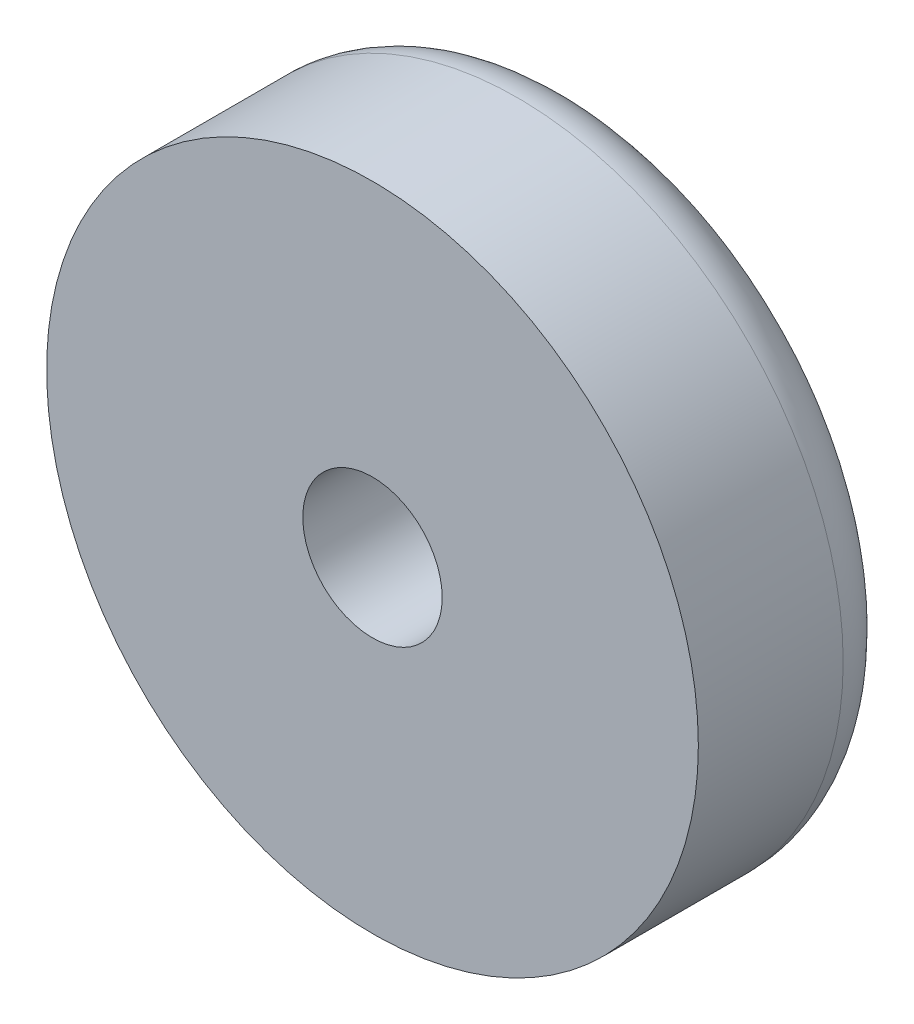
SolidWorks part; units mm, degrees
ref_plane "Front Plane" through (0, 0, 0) normal (0, 0, 1) x (1, 0, 0)
ref_plane "Top Plane" through (0, 0, 0) normal (0, 1, 0) x (1, 0, 0)
ref_plane "Right Plane" through (0, 0, 0) normal (1, 0, 0) x (0, 0, -1)
sketch "Sketch3" plane through (0, 0, 0) normal (0, 1, 0) x (1, 0, 0)
  line L0 (0, 0) -> (0, 3.16) construction
  line L1 (0, 3.16) -> (3.85, 3.16)
  line L2 (3.85, 0) -> (18, 0)
  line L3 (3.85, 3.16) -> (3.85, 0)
  line L4 (0, 3.16) -> (0, 4.26)
  line L5 (4.3, 3.376) -> (4.3, 1.616)
  line L6 (4.3, 1.616) -> (5, 1.616)
  line L7 (5, 1.616) -> (5, 2.2)
  line L8 (5, 2.2) -> (11.7, 2.2)
  line L9 (11.7, 2.2) -> (11.7, 1.74)
  line L10 (11.7, 1.74) -> (12.2, 1.74)
  line L11 (12.2, 1.74) -> (12.2, 1.8655)
  line L12 (0, 0) -> (3.85, 0) construction
  arc A0 (0, 4.26) -> (4.3, 3.376) centre (0, -6.64) cw
  arc A1 (12.2, 1.8655) -> (18, 0) centre (14.8, 0) cw
  dimension "D7" = 3.2
  dimension "D8" = 10.9
  dimension "D1" = 18
  dimension "D3" = 3.85
  dimension "D4" = 0.7
  dimension "D5" = 0.5
  dimension "D6" = 6.7
  dimension "D10" = 2.2
  dimension "D11" = 1.1
  dimension "D12" = 0.45
  dimension "D13" = 0.46
revolve "Revolve2" add sketch "Sketch3" angle 360 about L0
sketch "Sketch4" plane through (0, 0, 0) normal (0, 0, 1) x (1, 0, 0)
  circle A0 centre (0, 0) radius 3.85 construction
  circle A1 centre (0, 0) radius 18
  circle A2 centre (0, 0) radius 18
  circle A3 centre (0, 0) radius 3.85
  dimension "D1" = 0
extrude "Boss-Extrude1" add sketch "Sketch4" along normal blind 8
